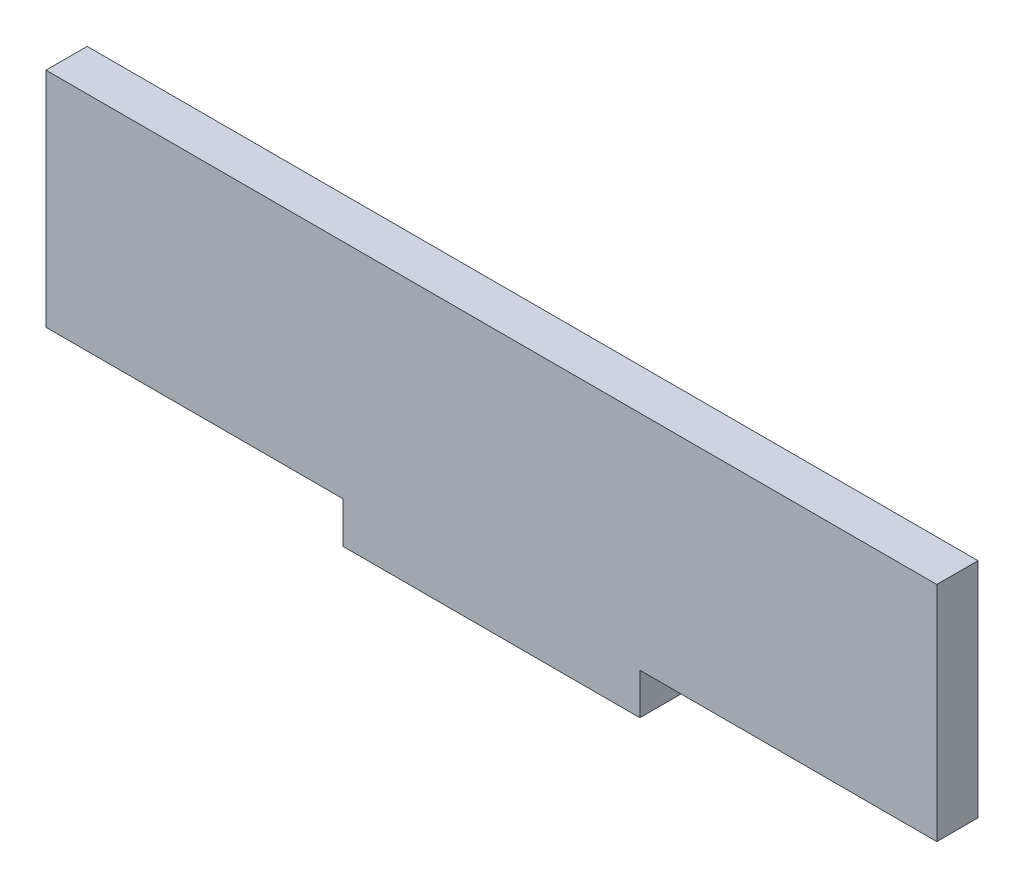
SolidWorks part; units mm, degrees
ref_plane "Front Plane" through (0, 0, 0) normal (0, 0, 1) x (1, 0, 0)
ref_plane "Top Plane" through (0, 0, 0) normal (0, 1, 0) x (1, 0, 0)
ref_plane "Right Plane" through (0, 0, 0) normal (1, 0, 0) x (0, 0, -1)
sketch "Sketch1" plane through (0, 0, 0) normal (0, 0, 1) x (1, 0, 0)
  line L0 (67.7333, 0) -> (101.6, 0)
  line L1 (0, 0) -> (33.8667, 0)
  line L2 (0, 0) -> (0, 25.4)
  line L3 (0, 25.4) -> (101.6, 25.4)
  line L4 (101.6, 0) -> (101.6, 25.4)
  line L6 (33.8667, 0) -> (33.8667, -4.699)
  line L7 (33.8667, -4.699) -> (67.7333, -4.699)
  line L8 (67.7333, 0) -> (67.7333, -4.699)
  dimension "D1" = 101.6
  dimension "D2" = 25.4
  dimension "D3" = 4.699
extrude "Boss-Extrude1" add sketch "Sketch1" along normal blind 4.699
equation "\"mat\"= \"mat@jaws.assembly\""
equation "\"D3@Sketch1\"= \"mat\""
equation "\"D1@Boss-Extrude1\"= \"mat\""
